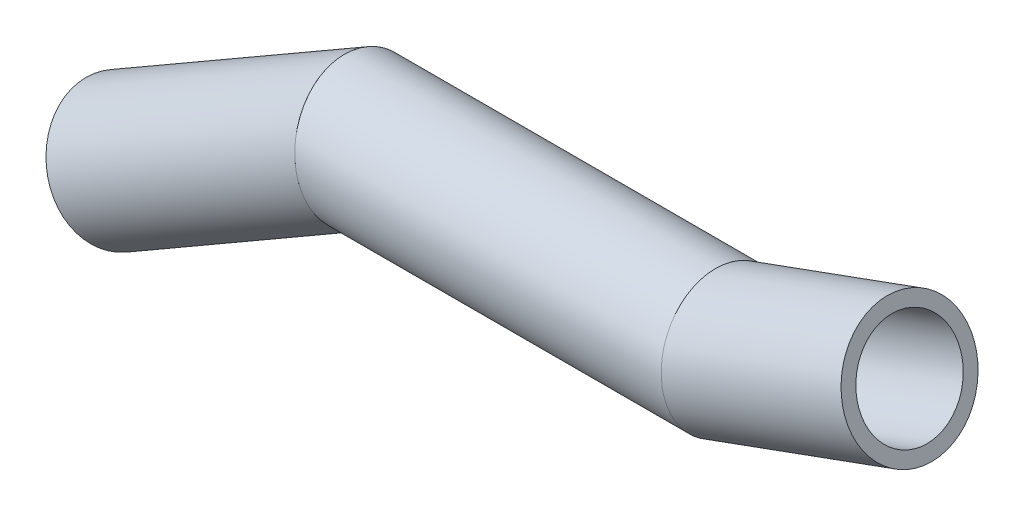
SolidWorks part; units mm, degrees
ref_plane "Alzado" through (0, 0, 0) normal (0, 0, 1) x (1, 0, 0)
ref_plane "Planta" through (0, 0, 0) normal (0, 1, 0) x (1, 0, 0)
ref_plane "Vista lateral" through (0, 0, 0) normal (1, 0, 0) x (0, 0, -1)
sketch "Croquis1" plane through (0, 0, 0) normal (0, 0, 1) x (1, 0, 0)
  line L0 (0, 0) -> (40, 23.094)
  line L1 (40, 23.094) -> (100, 23.094)
  line L2 (100, 23.094) -> (130, 34.0131)
  dimension "D1" = 40
  dimension "D2" = 60
  dimension "D3" = 30
  dimension "D4" = 30
  dimension "D5" = 20
other "Tubería 21.3 X 2.3(1)"
ref_plane "Plano1" through (0, 0, 0) normal (0.866, 0.5, 0) x (-0.5, 0.866, 0)
sketch "Sketch1" plane through (0, 0, 0) normal (0.866, 0.5, 0) x (-0.5, 0.866, 0)
  circle A0 centre (0, 0) radius 8.35
  circle A1 centre (0, 0) radius 10.65
  point P3 (0, 0)
  dimension "In_dia" = 16.7
  dimension "Out_dia" = 21.3
